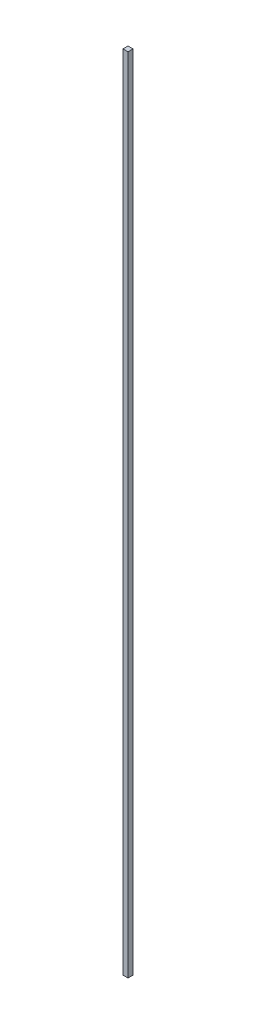
SolidWorks part; units mm, degrees
ref_plane "Front Plane" through (0, 0, 0) normal (0, 0, 1) x (1, 0, 0)
ref_plane "Top Plane" through (0, 0, 0) normal (0, 1, 0) x (1, 0, 0)
ref_plane "Right Plane" through (0, 0, 0) normal (1, 0, 0) x (0, 0, -1)
sketch "Sketch1" plane through (0, 0, 0) normal (0, 1, 0) x (1, 0, 0)
  line L1 (-3.2, 0) -> (0, 0)
  line L2 (-3.2, 0) -> (-3.2, -3.2)
  line L3 (-3.2, -3.2) -> (0, -3.2)
  line L4 (0, 0) -> (0, -3.2)
  dimension "D1" = 3.2
  dimension "D2" = 3.2
extrude "Boss-Extrude2" add sketch "Sketch1" along normal blind 510
